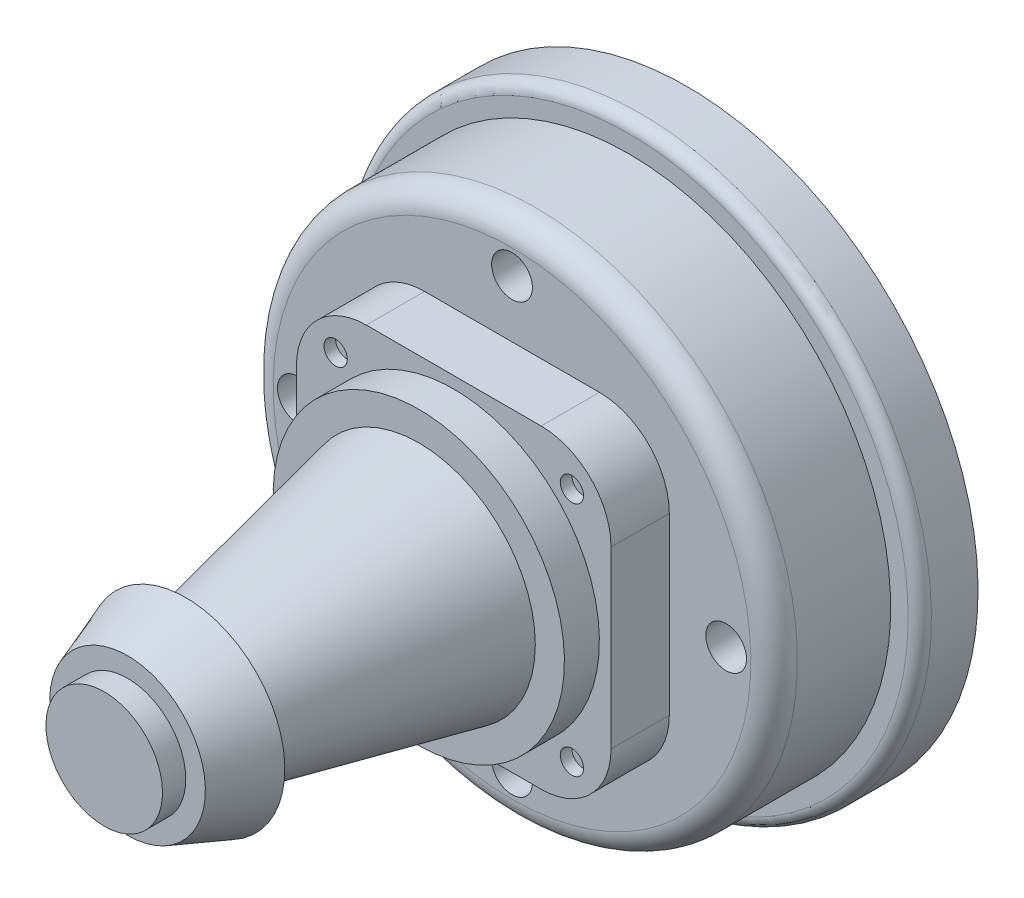
SolidWorks part; units mm, degrees
ref_plane "Front Plane" through (0, 0, 0) normal (0, 0, 1) x (1, 0, 0)
ref_plane "Top Plane" through (0, 0, 0) normal (0, 1, 0) x (1, 0, 0)
ref_plane "Right Plane" through (0, 0, 0) normal (1, 0, 0) x (0, 0, -1)
sketch "Sketch1" plane through (0, 0, 0) normal (0, 1, 0) x (1, 0, 0)
  circle A0 centre (0, 0) radius 25
  dimension "D1" = 50
extrude "Boss-Extrude1" add sketch "Sketch1" along normal blind 5 contours A0
sketch "Sketch2" plane through (0, 5, 0) normal (0, 1, 0) x (1, 0, 0)
  circle A0 centre (0, 0) radius 22.5
  dimension "D1" = 45
extrude "Boss-Extrude2" add sketch "Sketch2" along normal blind 10
sketch "Sketch3" plane through (0, 15, 0) normal (0, 1, 0) x (1, 0, 0)
  line L1 (-13.5, 13.5) -> (13.5, 13.5)
  line L2 (-13.5, 13.5) -> (-13.5, -13.5)
  line L3 (-13.5, -13.5) -> (13.5, -13.5)
  line L4 (13.5, 13.5) -> (13.5, -13.5)
  line L5 (-13.5, 13.5) -> (13.5, -13.5) construction
  line L6 (-13.5, -13.5) -> (13.5, 13.5) construction
  point P0 (0, 0)
  dimension "D1" = 27
  dimension "D2" = 27
extrude "Boss-Extrude3" add sketch "Sketch3" along normal blind 5
sketch "Sketch5" plane through (0, 20, 0) normal (0, 1, 0) x (1, 0, 0)
  circle A0 centre (0, 0) radius 12.5
  dimension "D1" = 25
extrude "Boss-Extrude4" add sketch "Sketch5" along normal blind 3
sketch "Sketch6" plane through (0, 23, 0) normal (0, 1, 0) x (1, 0, 0)
  circle A0 centre (0, 0) radius 10
  dimension "D1" = 20
extrude "Boss-Extrude5" add sketch "Sketch6" along normal blind 20 draft 12
sketch "Sketch7" plane through (0, 43, 0) normal (0, 1, 0) x (1, 0, 0)
  circle A0 centre (0, 0) radius 8.5
  dimension "D1" = 17
extrude "Boss-Extrude6" add sketch "Sketch7" along normal blind 5 draft 20
sketch "Sketch8" plane through (0, 48, 0) normal (0, 1, 0) x (1, 0, 0)
  circle A0 centre (0, 0) radius 5
  dimension "D1" = 10
extrude "Boss-Extrude7" add sketch "Sketch8" along normal blind 2
fillet "Fillet1" radius 6 4 edges at (13.5, 17.5, 13.5) (-13.5, 17.5, 13.5) (13.5, 17.5, -13.5) (-13.5, 17.5, -13.5)
sketch "Sketch10" plane through (0, 15, 0) normal (0, 1, 0) x (1, 0, 0)
  line L0 (0, 0) -> (-18.3794, 0)
  line L1 (0, 0) -> (0, 18.4002)
  circle A0 centre (-18.3794, 0) radius 1.75
  circle A1 centre (0, 18.4002) radius 1.75
  dimension "D1" = 3.5
  dimension "D2" = 3.5
extrude "Cut-Extrude2" cut sketch "Sketch10" against normal blind 5 contours A0 | A1
sketch "Sketch11" plane through (0, 20, 0) normal (0, 1, 0) x (1, 0, 0)
  line L0 (0, 0) -> (10.1393, 10.1393)
  line L1 (0, 0) -> (-10.1393, 10.1393)
  circle A0 centre (10.1393, 10.1393) radius 1
  circle A1 centre (-10.1393, 10.1393) radius 1
  dimension "D1" = 2
  dimension "D2" = 2
extrude "Cut-Extrude3" cut sketch "Sketch11" against normal blind 1 contours A1 | A0
mirror "Mirror4" about plane through (0, 0, 0) normal (0, 0, 1) of "Cut-Extrude2", "Cut-Extrude3"
mirror "Mirror6" about plane through (0, 0, 0) normal (1, 0, 0) of "Cut-Extrude2"
sketch "Sketch12" plane through (0, 0, 0) normal (0, -1, 0) x (1, 0, 0)
  circle A0 centre (0, 0) radius 10
  dimension "D1" = 20
extrude "Cut-Extrude4" cut sketch "Sketch12" against normal blind 5
fillet "Fillet2" radius 2 1 edges at (0, 15, 22.5)
fillet "Fillet3" radius 1 1 edges at (0, 5, 25)
sketch "Sketch13" plane through (0, 5, 0) normal (0, -1, 0) x (1, 0, 0)
  point P0 (0, 0)
move or copy body "Body-Move/Copy1" bodies to move or copy 117 copy no translate (0, -5, 0)
move or copy body "Body-Move/Copy2" bodies to move or copy 118 copy no rotation origin (0, 0, 0) rotation axis (1, 0, 0) rotation angle 90
